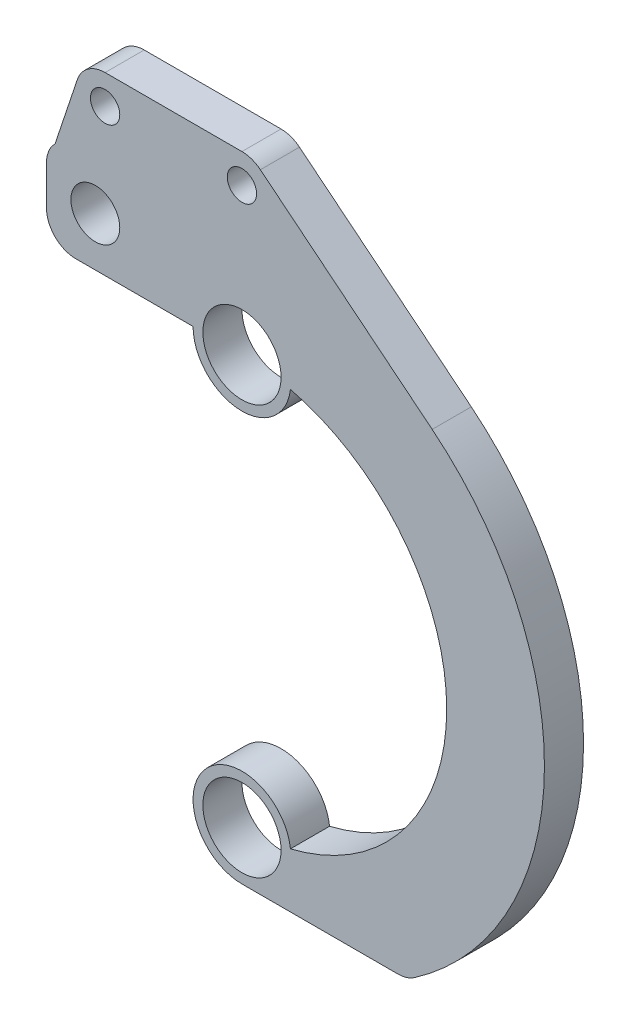
SolidWorks part; units mm, degrees
ref_plane "Alzado" through (0, 0, 0) normal (0, 0, 1) x (1, 0, 0)
ref_plane "Planta" through (0, 0, 0) normal (0, 1, 0) x (1, 0, 0)
ref_plane "Vista lateral" through (0, 0, 0) normal (1, 0, 0) x (0, 0, -1)
sketch "Croquis1" plane through (0, 0, 0) normal (0, 0, 1) x (1, 0, 0)
  line L0 (0, 0) -> (0, -20.95) construction
  line L1 (0, 0) -> (0, 20.95) construction
  line L2 (-20, 25.95) -> (-15, 25.95) construction
  line L3 (0, 20.95) -> (-4, 20.95)
  line L4 (0, 20.95) -> (0, 24.95)
  line L5 (0, 30.95) -> (-17, 30.95)
  line L6 (-20, 23.95) -> (-20, 27.95)
  line L7 (0, -25.95) -> (15.9531, -25.95)
  line L8 (-5, 20.95) -> (-17, 20.95)
  line L9 (0, 0) -> (18.3494, 18.3494) construction
  line L10 (0, 0) -> (25.95, 0) construction
  line L11 (-14, 30.95) -> (-14, 32.95) construction
  line L12 (0, 30.95) -> (0, 35.95) construction
  line L13 (0, 35.95) -> (-14, 35.95) construction
  line L14 (-16.8461, 36.8985) -> (-19.1213, 30.0713)
  line L15 (-14, 38.95) -> (0, 38.95)
  line L16 (1.8868, 38.2824) -> (19.4651, 24.0627)
  line L17 (-14, 34.45) -> (-14, 35.95) construction
  arc A0 (-3.9817, -20.5681) -> (3.9817, -20.5681) centre (0, 0) ccw
  arc A1 (17.6654, -25.4133) -> (0, 30.95) centre (0, 0) ccw
  arc A2 (-5, 20.95) -> (4.9643, 20.3533) centre (0, 20.95) ccw
  arc A3 (4.9643, -20.3533) -> (0, -25.95) centre (0, -20.95) ccw
  circle A4 centre (0, 20.95) radius 4
  circle A5 centre (0, -20.95) radius 4
  circle A6 centre (-15, 25.95) radius 2.5
  circle A7 centre (0, 0) radius 25.95 construction
  arc A8 (4.9643, -20.3533) -> (4.9643, 20.3533) centre (0, 0) ccw
  arc A11 (15.9531, -25.95) -> (17.6654, -25.4133) centre (15.9531, -22.95) ccw
  arc A12 (-17, 20.95) -> (-20, 23.95) centre (-17, 23.95) cw
  arc A13 (-17, 30.95) -> (-20, 27.95) centre (-17, 27.95) ccw
  circle A14 centre (-14, 35.95) radius 1.5
  circle A15 centre (0, 35.95) radius 1.5
  arc A16 (-14, 38.95) -> (-16.8461, 36.8985) centre (-14, 35.95) ccw
  arc A17 (1.8868, 38.2824) -> (0, 38.95) centre (0, 35.95) ccw
  point P32 (-20, 30.95)
  dimension "D1" = 41.9
  dimension "D3" = 10
  dimension "D4" = 10
  dimension "D5" = 10
  dimension "D6" = 8
  dimension "D7" = 8
  dimension "D9" = 5
  dimension "D12" = 5
  dimension "D17" = 3
  dimension "D18" = 5
  dimension "D19" = 3
  dimension "D20" = 3
  dimension "D22" = 6
  dimension "D2" = 180
  dimension "D8" = 20
  dimension "D10" = 5
  dimension "D11" = 90
  dimension "D15" = 45
  dimension "D16" = 45
  dimension "D21" = 6
extrude "Saliente-Extruir1" add sketch "Croquis1" along normal blind 4 contours A8 A3 L7 A1 L5 L6 L8 A2 A6 A5 A4 | L16 A17 L15 A16 L14 A13 L5 A1 A14 A15
